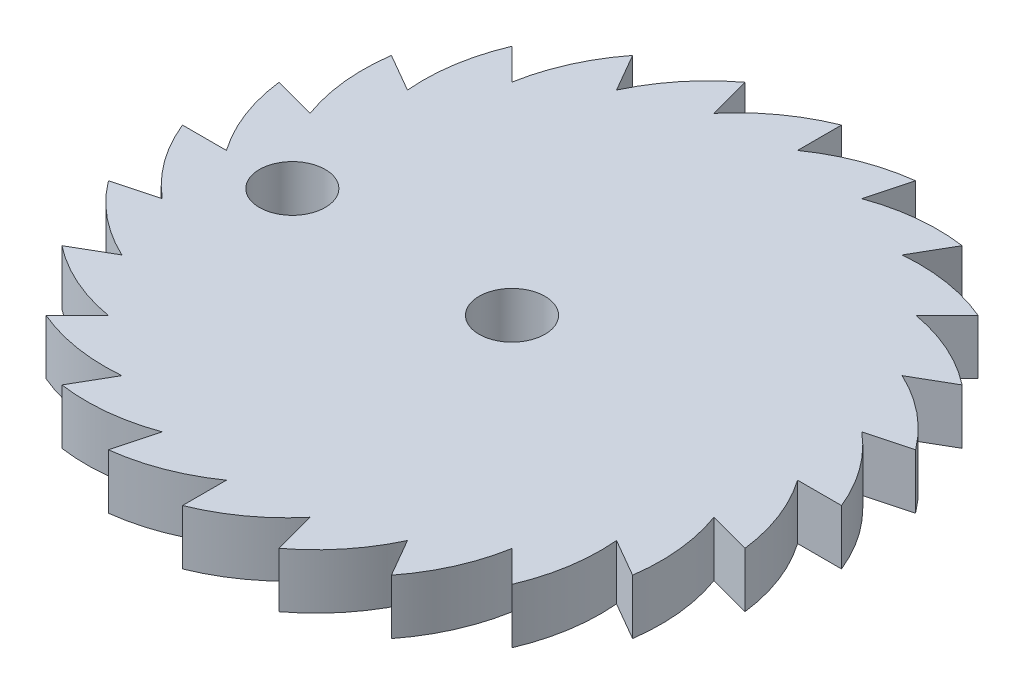
SolidWorks part; units mm, degrees
ref_plane "前视基准面" through (0, 0, 0) normal (0, 0, 1) x (1, 0, 0)
ref_plane "上视基准面" through (0, 0, 0) normal (0, 1, 0) x (1, 0, 0)
ref_plane "右视基准面" through (0, 0, 0) normal (1, 0, 0) x (0, 0, -1)
sketch "草图1" plane through (0, 0, 0) normal (0, 1, 0) x (1, 0, 0)
  line L0 (0, 13) -> (3.8823, 14.4889)
  line L1 (0, 0) -> (0, 15) construction
  line L2 (0, 0) -> (3.8823, 14.4889) construction
  line L3 (3.8823, 14.4889) -> (3.3646, 12.557)
  line L4 (7.5, 12.9904) -> (6.5, 11.2583)
  line L5 (10.6066, 10.6066) -> (9.1924, 9.1924)
  line L6 (12.9904, 7.5) -> (11.2583, 6.5)
  line L7 (14.4889, 3.8823) -> (12.557, 3.3646)
  line L8 (15, 0) -> (13, 0)
  line L9 (14.4889, -3.8823) -> (12.557, -3.3646)
  line L10 (12.9904, -7.5) -> (11.2583, -6.5)
  line L11 (10.6066, -10.6066) -> (9.1924, -9.1924)
  line L12 (7.5, -12.9904) -> (6.5, -11.2583)
  line L13 (3.8823, -14.4889) -> (3.3646, -12.557)
  line L14 (0, -15) -> (0, -13)
  line L15 (-3.8823, -14.4889) -> (-3.3646, -12.557)
  line L16 (-7.5, -12.9904) -> (-6.5, -11.2583)
  line L17 (-10.6066, -10.6066) -> (-9.1924, -9.1924)
  line L18 (-12.9904, -7.5) -> (-11.2583, -6.5)
  line L19 (-14.4889, -3.8823) -> (-12.557, -3.3646)
  line L20 (-15, 0) -> (-13, 0)
  line L21 (-14.4889, 3.8823) -> (-12.557, 3.3646)
  line L22 (-12.9904, 7.5) -> (-11.2583, 6.5)
  line L23 (-10.6066, 10.6066) -> (-9.1924, 9.1924)
  line L24 (-7.5, 12.9904) -> (-6.5, 11.2583)
  line L25 (-3.8823, 14.4889) -> (-3.3646, 12.557)
  line L26 (0, 15) -> (0, 13)
  circle A0 centre (0, 0) radius 15
  circle A1 centre (0, 0) radius 10
  circle A2 centre (-10, 0) radius 1.5
  circle A3 centre (0, 0) radius 13
  arc A4 (0, 13) -> (3.8823, 14.4889) centre (4.9145, 5.9915) cw
  arc A5 (3.3646, 12.557) -> (7.5, 12.9904) centre (6.2977, 4.5154) cw
  arc A6 (6.5, 11.2583) -> (10.6066, 10.6066) centre (7.2518, 2.7315) cw
  arc A7 (9.1924, 9.1924) -> (12.9904, 7.5) centre (7.7117, 0.7616) cw
  arc A8 (11.2583, 6.5) -> (14.4889, 3.8823) centre (7.646, -1.2603) cw
  arc A9 (12.557, 3.3646) -> (15, 0) centre (7.0593, -3.1963) cw
  arc A10 (13, 0) -> (14.4889, -3.8823) centre (5.9915, -4.9145) cw
  arc A11 (12.557, -3.3646) -> (12.9904, -7.5) centre (4.5154, -6.2977) cw
  arc A12 (11.2583, -6.5) -> (10.6066, -10.6066) centre (2.7315, -7.2518) cw
  arc A13 (9.1924, -9.1924) -> (7.5, -12.9904) centre (0.7616, -7.7117) cw
  arc A14 (6.5, -11.2583) -> (3.8823, -14.4889) centre (-1.2603, -7.646) cw
  arc A15 (3.3646, -12.557) -> (0, -15) centre (-3.1963, -7.0593) cw
  arc A16 (0, -13) -> (-3.8823, -14.4889) centre (-4.9145, -5.9915) cw
  arc A17 (-3.3646, -12.557) -> (-7.5, -12.9904) centre (-6.2977, -4.5154) cw
  arc A18 (-6.5, -11.2583) -> (-10.6066, -10.6066) centre (-7.2518, -2.7315) cw
  arc A19 (-9.1924, -9.1924) -> (-12.9904, -7.5) centre (-7.7117, -0.7616) cw
  arc A20 (-11.2583, -6.5) -> (-14.4889, -3.8823) centre (-7.646, 1.2603) cw
  arc A21 (-12.557, -3.3646) -> (-15, 0) centre (-7.0593, 3.1963) cw
  arc A22 (-13, 0) -> (-14.4889, 3.8823) centre (-5.9915, 4.9145) cw
  arc A23 (-12.557, 3.3646) -> (-12.9904, 7.5) centre (-4.5154, 6.2977) cw
  arc A24 (-11.2583, 6.5) -> (-10.6066, 10.6066) centre (-2.7315, 7.2518) cw
  arc A25 (-9.1924, 9.1924) -> (-7.5, 12.9904) centre (-0.7616, 7.7117) cw
  arc A26 (-6.5, 11.2583) -> (-3.8823, 14.4889) centre (1.2603, 7.646) cw
  arc A27 (-3.3646, 12.557) -> (0, 15) centre (3.1963, 7.0593) cw
  circle A28 centre (0, 0) radius 1.5
  point P13 (0, 13)
  point P108 (0, 0)
  dimension "D1" = 30
  dimension "D2" = 20
  dimension "D3" = 3
  dimension "D4" = 26
  dimension "D6" = 4.2
  dimension "D8" = 3
  dimension "D5" = 15
  dimension "D7" = 24
extrude "凸台-拉伸1" add sketch "草图1" along normal blind 2.5 contours A3 A2 A1 | A2 A1 A28 | A23 A3 L22 | A22 A3 L21 | A21 A3 L20 | A20 A3 L19 | A19 A3 L18 | A18 A3 L17 | A17 A3 L16 | A16 A3 L15 | A15 A3 L14 | A14 A3 L13 | A13 A3 L12 | A12 A3 L11 | A11 A3 L10 | A10 A3 L9 | A9 A3 L8 | A8 A3 L7 | A7 A3 L6 | A6 A3 L5 | A5 A3 L4 | A27 A3 L26 | A26 A3 L25 | A25 A3 L24 | A24 A3 L23 | A4 L0 | A3 L3 L0
